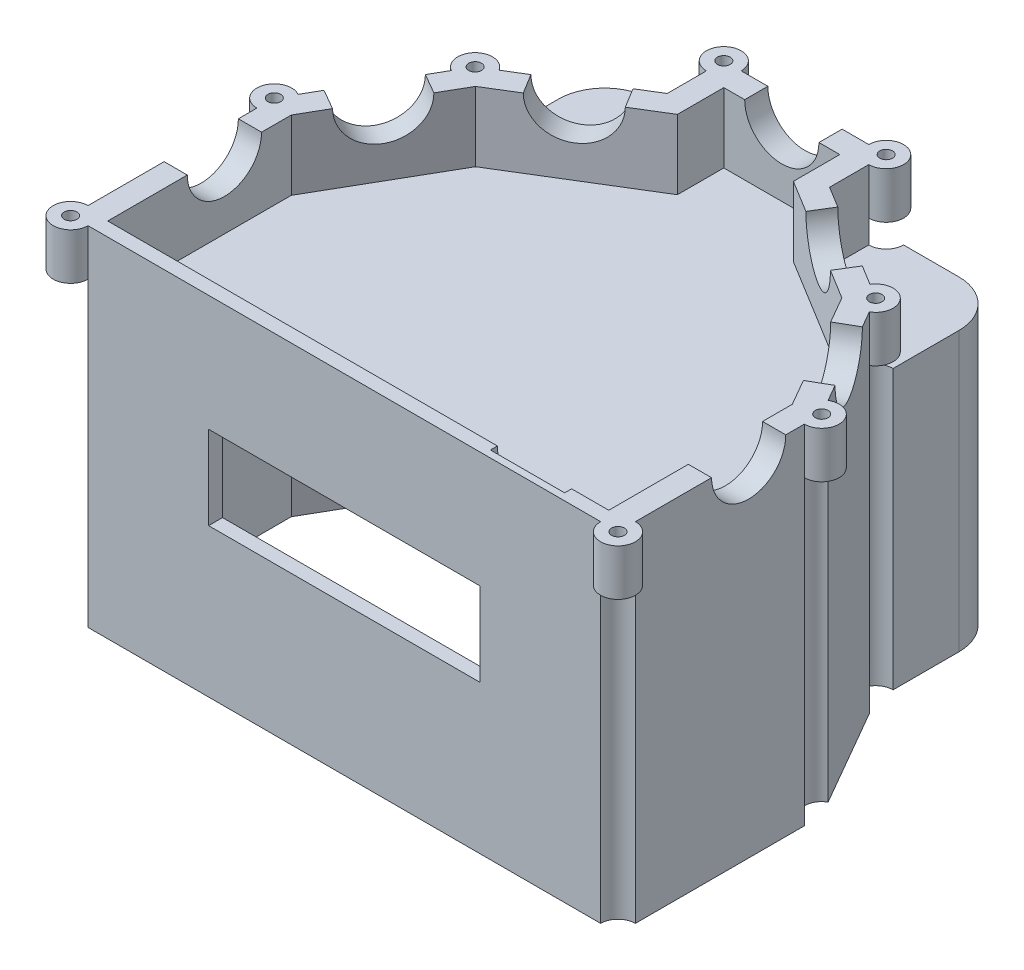
SolidWorks part; units mm, degrees
ref_plane "Front Plane" through (0, 0, 0) normal (0, 0, 1) x (1, 0, 0)
ref_plane "Top Plane" through (0, 0, 0) normal (0, 1, 0) x (1, 0, 0)
ref_plane "Right Plane" through (0, 0, 0) normal (1, 0, 0) x (0, 0, -1)
sketch "Sketch1" plane through (0, 0, 0) normal (0, 1, 0) x (1, 0, 0)
  line L0 (-50, -32.5) -> (50, -32.5)
  line L1 (50, -32.5) -> (50, 0)
  line L2 (50, 0) -> (36.5236, 23.3963)
  line L3 (36.5236, 23.3963) -> (13.5, 37.5)
  line L4 (13.5, 37.5) -> (-13.5, 37.5)
  line L5 (-13.5, 37.5) -> (-36.5236, 23.3963)
  line L6 (-36.5236, 23.3963) -> (-50, 0)
  line L7 (-50, 0) -> (-50, -32.5)
  line L8 (-43.1787, 29.8739) -> (-17.5, 45.6041)
  line L10 (17.5, 45.6041) -> (43.1787, 29.8739)
  line L11 (43.1787, 29.8739) -> (59, 2.4067)
  line L12 (-43.1787, 29.8739) -> (-59, 2.4067)
  line L13 (-59, 2.4067) -> (-59, -41.5)
  line L14 (-59, -41.5) -> (59, -41.5)
  line L15 (59, -41.5) -> (59, 2.4067)
  line L16 (-50, 0) -> (50, 0) construction
  line L17 (-13.5, 37.5) -> (0, 0) construction
  line L18 (0, 0) -> (13.5, 37.5) construction
  line L19 (0, 0) -> (36.5236, 23.3963) construction
  line L20 (-36.5236, 23.3963) -> (0, 0) construction
  line L21 (39.4814, 26.2752) -> (12.5, 42.8034)
  line L23 (-12.5, 42.8034) -> (-39.4814, 26.2752)
  line L24 (-39.4814, 26.2752) -> (-54, 1.0696)
  line L25 (-54, 1.0696) -> (-54, -38.5)
  line L26 (-54, -38.5) -> (54, -38.5)
  line L27 (54, -38.5) -> (54, 1.0696)
  line L28 (54, 1.0696) -> (39.4814, 26.2752)
  line L29 (17.5, 45.6041) -> (17.5, 57.8034)
  line L30 (17.5, 57.8034) -> (-17.5, 57.8034)
  line L31 (-17.5, 57.8034) -> (-17.5, 45.6041)
  line L32 (12.5, 42.8034) -> (12.5, 52.8034)
  line L33 (12.5, 52.8034) -> (-12.5, 52.8034)
  line L34 (-12.5, 52.8034) -> (-12.5, 42.8034)
  dimension "D4" = 10
  dimension "D1" = 100
  dimension "D2" = 70
  dimension "D3" = 27
  dimension "D5" = 27
  dimension "D7" = 27
  dimension "D8" = 32.5
  dimension "D16" = 5
  dimension "D17" = 9
  dimension "D18" = 9
  dimension "D19" = 9
  dimension "D20" = 9
  dimension "D21" = 9
  dimension "D22" = 9
  dimension "D23" = 9
  dimension "D24" = 5
  dimension "D25" = 5
  dimension "D26" = 5
  dimension "D27" = 5
  dimension "D28" = 3
  dimension "D29" = 5
  dimension "D30" = 5
  dimension "D31" = 5
  dimension "D32" = 5
  dimension "D33" = 25
extrude "Boss-Extrude2" add sketch "Sketch1" along normal blind 15 contours L8 L31 L30 L29 L10 L11 L15 L14 L13 L12 | L34 L23 L24 L25 L26 L27 L28 L21 L32 L33
sketch "Sketch2" plane through (0, 0, 0) normal (0, -1, 0) x (1, 0, 0)
  line L4 (-59, -2.4067) -> (-59, 41.5)
  line L5 (-59, 41.5) -> (59, 41.5)
  line L6 (59, 41.5) -> (59, -2.4067)
  line L15 (59, -2.4067) -> (43.1787, -29.8739)
  line L16 (43.1787, -29.8739) -> (43.1787, -57.8034)
  line L17 (43.1787, -57.8034) -> (-43.1787, -57.8034)
  line L18 (-43.1787, -57.8034) -> (-43.1787, -29.8739)
  line L19 (-43.1787, -29.8739) -> (-59, -2.4067)
  line L20 (17.5, -57.8034) -> (-17.5, -57.8034) construction
  dimension "D1" = 0
extrude "Boss-Extrude3" add sketch "Sketch2" along normal blind 5
sketch "Sketch7" plane through (0, 15, 0) normal (0, 1, 0) x (1, 0, 0)
  circle A0 centre (-59, -41.5) radius 3.75
  circle A1 centre (-59, 2.4067) radius 3.75
  circle A2 centre (-43.1787, 29.8739) radius 3.75
  circle A4 centre (-17.5, 57.8034) radius 3.75
  circle A5 centre (17.5, 57.8034) radius 3.75
  circle A7 centre (43.1787, 29.8739) radius 3.75
  circle A8 centre (59, 2.4067) radius 3.75
  circle A9 centre (59, -41.5) radius 3.75
  dimension "D1" = 7.5
extrude "Boss-Extrude9" add sketch "Sketch7" against normal blind 10
sketch "Sketch9" plane through (0, 15, 0) normal (0, 1, 0) x (1, 0, 0)
  circle A0 centre (-59, -41.5) radius 1.375
  circle A1 centre (-59, 2.4067) radius 1.375
  circle A2 centre (-17.5, 57.8034) radius 1.375
  circle A4 centre (43.1787, 29.8739) radius 1.375
  circle A6 centre (17.5, 57.8034) radius 1.375
  circle A7 centre (-43.1787, 29.8739) radius 1.375
  circle A8 centre (59, 2.4067) radius 1.375
  circle A9 centre (59, -41.5) radius 1.375
  dimension "D1" = 2.75
extrude "Cut-Extrude5" cut sketch "Sketch9" against normal through all
sketch "Sketch14" plane through (-45.3424, 0, -26.1175) normal (-0.8665, 0, -0.4991) x (-0.4991, 0, 0.8665)
  line L0 (-0.585, 15) -> (23.613, 15) construction
  circle A0 centre (11.514, 15) radius 8
  dimension "D1" = 16
extrude "Cut-Extrude9" cut sketch "Sketch14" against normal up to next
sketch "Sketch16" plane through (0, 0, -57.8034) normal (0, 0, -1) x (-1, 0, 0)
  line L0 (-13.75, 15) -> (13.75, 15) construction
  circle A0 centre (0, 15) radius 8
  dimension "D1" = 16
extrude "Cut-Extrude11" cut sketch "Sketch16" against normal up to next
sketch "Sketch17" plane through (45.3424, 0, -26.1175) normal (0.8665, 0, -0.4991) x (-0.4991, 0, -0.8665)
  line L0 (0.585, 15) -> (-23.613, 15) construction
  circle A0 centre (-11.514, 15) radius 8
  dimension "D1" = 16
extrude "Cut-Extrude12" cut sketch "Sketch17" against normal up to next
sketch "Sketch19" plane through (-25.0884, 0, -40.9556) normal (-0.5224, 0, -0.8527) x (-0.8527, 0, 0.5224)
  line L0 (17.4646, 15) -> (-8.8991, 15) construction
  line L1 (17.4646, 15) -> (17.4646, 5) construction
  circle A0 centre (4.4646, 15) radius 8
  dimension "D1" = 16
  dimension "D2" = 13
extrude "Cut-Extrude13" cut sketch "Sketch19" against normal up to next
sketch "Sketch20" plane through (25.0884, 0, -40.9556) normal (0.5224, 0, -0.8527) x (-0.8527, 0, -0.5224)
  line L0 (8.8991, 15) -> (-17.4646, 15) construction
  line L1 (-17.4646, 5) -> (-17.4646, 15) construction
  circle A0 centre (-4.4646, 15) radius 8
  dimension "D1" = 16
  dimension "D2" = 13
extrude "Cut-Extrude14" cut sketch "Sketch20" against normal up to next
sketch "Sketch21" plane through (0, -5, 0) normal (0, -1, 0) x (1, 0, 0)
  line L0 (59, 41.5) -> (59, -2.4067)
  line L4 (-59, -2.4067) -> (-59, 41.5)
  line L5 (-59, 41.5) -> (59, 41.5)
  line L6 (54, 38.5) -> (-54, 38.5)
  line L7 (-54, 38.5) -> (-54, -1.0696)
  line L8 (-54, -1.0696) -> (-38.1787, -28.5369)
  line L10 (38.1787, -28.5369) -> (54, -1.0696)
  line L11 (54, -1.0696) -> (54, 38.5)
  line L16 (-59, -2.4067) -> (-43.1787, -29.8739)
  line L18 (59, -2.4067) -> (43.1787, -29.8739)
  line L20 (38.1787, -28.5369) -> (38.1787, -52.8034)
  line L21 (38.1787, -52.8034) -> (-38.1787, -52.8034)
  line L22 (-38.1787, -52.8034) -> (-38.1787, -28.5369)
  line L27 (43.1787, -29.8739) -> (43.1787, -57.8034)
  line L28 (43.1787, -57.8034) -> (-43.1787, -57.8034)
  line L29 (-43.1787, -57.8034) -> (-43.1787, -29.8739)
  dimension "D1" = 5
  dimension "D2" = 3
  dimension "D3" = 5
  dimension "D4" = 5
  dimension "D5" = 5
  dimension "D6" = 5
  dimension "D8" = 5
  dimension "D9" = 5
extrude "Boss-Extrude11" add sketch "Sketch21" along normal blind 55
sketch "Sketch24" plane through (0, -60, 0) normal (0, -1, 0) x (1, 0, 0)
  circle A0 centre (59, 41.5) radius 3.75
  circle A1 centre (59, -2.4067) radius 3.75
  circle A2 centre (43.1787, -29.8739) radius 3.75
  circle A3 centre (17.5, -57.8034) radius 3.75
  circle A4 centre (-17.5, -57.8034) radius 3.75
  circle A5 centre (-43.1787, -29.8739) radius 3.75
  circle A6 centre (-59, -2.4067) radius 3.75
  circle A7 centre (-59, 41.5) radius 3.75
  dimension "D1" = 7.5
fillet "Fillet1" radius 10 2 edges at (-43.1787, -30, -57.8034) (43.1787, -30, -57.8034)
sketch "Sketch25" plane through (0, -5, 0) normal (0, -1, 0) x (-1, 0, 0)
  line L0 (-54, -38.5) -> (54, -38.5) construction
  circle A0 centre (-24.5, 40.5) radius 1.4
  circle A1 centre (24.5, 40.5) radius 1.4
  circle A2 centre (24.5, -17.5) radius 1.4
  circle A3 centre (-24.5, -17.5) radius 1.4
  circle A4 centre (-24.5, 40.5) radius 4
  circle A5 centre (24.5, 40.5) radius 4
  circle A6 centre (24.5, -17.5) radius 4
  circle A7 centre (-24.5, -17.5) radius 4
  dimension "D1" = 2.8
  dimension "D2" = 58
  dimension "D4" = 49
  dimension "D6" = 49
  dimension "D7" = 0
  dimension "D8" = 58
  dimension "D9" = 0
  dimension "D10" = 8
  dimension "D3" = 21
  dimension "D5" = 24.5
extrude "Boss-Extrude12" add sketch "Sketch25" along normal blind 5
extrude "Cut-Extrude15" cut sketch "Sketch24" against normal blind 65
sketch "Sketch26" plane through (0, 0, 41.5) normal (0, 0, 1) x (1, 0, 0)
  line L0 (55.25, -60) -> (-55.25, -60) construction
  line L1 (29.25, -28) -> (-29.25, -28)
  line L2 (29.25, -28) -> (29.25, -10)
  line L3 (29.25, -10) -> (-29.25, -10)
  line L4 (-29.25, -28) -> (-29.25, -10)
  line L5 (29.25, -28) -> (-29.25, -10) construction
  line L6 (29.25, -10) -> (-29.25, -28) construction
  point P0 (0, -19)
  point P8 (0, -60)
  dimension "D1" = 18
  dimension "D2" = 58.5
  dimension "D3" = 0
  dimension "D4" = 50
extrude "Cut-Extrude17" cut sketch "Sketch26" against normal up to next
sketch "Sketch27" plane through (0, -60, 0) normal (0, -1, 0) x (-1, 0, 0)
  line L4 (38.1787, 52.8034) -> (-38.1787, 52.8034) construction
  line L5 (-38.1787, 52.8034) -> (-38.1787, 28.5369) construction
  line L6 (38.1787, 52.8034) -> (-38.1787, 52.8034) construction
  line L7 (38.1787, 28.5369) -> (38.1787, 52.8034) construction
  line L8 (54, -38.5) -> (54, 1.0696) construction
  line L9 (-54, -38.5) -> (54, -38.5) construction
  line L10 (-54, -38.5) -> (54, -38.5) construction
  line L11 (-54, 1.0696) -> (-54, -38.5) construction
  circle A0 centre (-51.25, -35.75) radius 4
  circle A1 centre (-35.4287, 50.0534) radius 4
  circle A2 centre (35.4287, 50.0534) radius 4
  circle A3 centre (51.25, -35.75) radius 4
  dimension "D1" = 8
  dimension "D2" = 2.75
  dimension "D3" = 2.75
  dimension "D4" = 2.75
  dimension "D5" = 2.75
  dimension "D6" = 2.75
  dimension "D7" = 2.75
  dimension "D8" = 2.75
  dimension "D9" = 2.75
extrude "Boss-Extrude13" add sketch "Sketch27" against normal up to next
sketch "Sketch28" plane through (0, -60, 0) normal (0, -1, 0) x (-1, 0, 0)
  circle A0 centre (-51.25, -35.75) radius 1.375
  circle A1 centre (-35.4287, 50.0534) radius 1.375
  circle A2 centre (35.4287, 50.0534) radius 1.375
  circle A3 centre (51.25, -35.75) radius 1.375
  dimension "D1" = 2.75
extrude "Cut-Extrude18" cut sketch "Sketch28" against normal blind 25
ref_plane "Plane1" through (-59, 15, 1.3433) normal (0, 0, 1) x (1, 0, 0)
sketch "Sketch30" plane through (-59, 0, 0) normal (-1, 0, 0) x (0, 0, 1)
  line L0 (1.3433, 15) -> (37.75, 15) construction
  circle A0 centre (13.34, 15) radius 8
  dimension "D1" = 25.16
extrude "Cut-Extrude19" cut sketch "Sketch30" against normal through all
sketch "Sketch31" plane through (0, 0, 38.5) normal (0, 0, -1) x (-1, 0, 0)
  line L0 (54, 15) -> (-54, 15) construction
  line L1 (-54, 15) -> (-54, 0) construction
  circle A0 centre (-38, 15) radius 8
  dimension "D2" = 16
  dimension "D1" = 16
extrude "Cut-Extrude20" cut sketch "Sketch31" against normal blind 1.5
sketch "Sketch33" plane through (0, -60, 0) normal (0, -1, 0) x (1, 0, 0)
  line L0 (-32.5239, -52.8034) -> (32.5239, -52.8034) construction
  line L2 (-13.5, -50.8034) -> (13.5, -50.8034)
  line L3 (-13.5, -50.8034) -> (-13.5, -54.8034)
  line L4 (-13.5, -54.8034) -> (13.5, -54.8034)
  line L5 (13.5, -50.8034) -> (13.5, -54.8034)
  line L6 (-13.5, -50.8034) -> (13.5, -54.8034) construction
  line L7 (-13.5, -54.8034) -> (13.5, -50.8034) construction
  point P2 (0, -52.8034)
  dimension "D1" = 27
  dimension "D2" = 4
extrude "Cut-Extrude21" cut sketch "Sketch33" against normal blind 40
sketch "Sketch35" plane through (0, 0, -54.8034) normal (0, 0, 1) x (1, 0, 0)
  line L1 (-13.5, -20) -> (13.5, -20) construction
  line L2 (13.5, -20) -> (13.5, -60) construction
  line L7 (4.5, -40) -> (-4.5, -40)
  line L8 (4.5, -40) -> (4.5, -31)
  line L9 (4.5, -31) -> (-4.5, -31)
  line L10 (-4.5, -40) -> (-4.5, -31)
  line L11 (4.5, -40) -> (-4.5, -31) construction
  line L12 (4.5, -31) -> (-4.5, -40) construction
  circle A4 centre (10.5, -35.5) radius 1.25
  circle A5 centre (-10.5, -35.5) radius 1.25
  circle A6 centre (-10.5, -23) radius 1.25
  circle A7 centre (10.5, -23) radius 1.25
  point P12 (0, -35.5)
  dimension "D1" = 2.5
  dimension "D4" = 21
  dimension "D5" = 12.5
  dimension "D6" = 0
  dimension "D7" = 0
  dimension "D8" = 12.5
  dimension "D9" = 21
  dimension "D2" = 3
  dimension "D3" = 3
  dimension "D10" = 9
  dimension "D11" = 9
  dimension "D12" = 9
  dimension "D13" = 11
extrude "Cut-Extrude22" cut sketch "Sketch35" against normal through all
